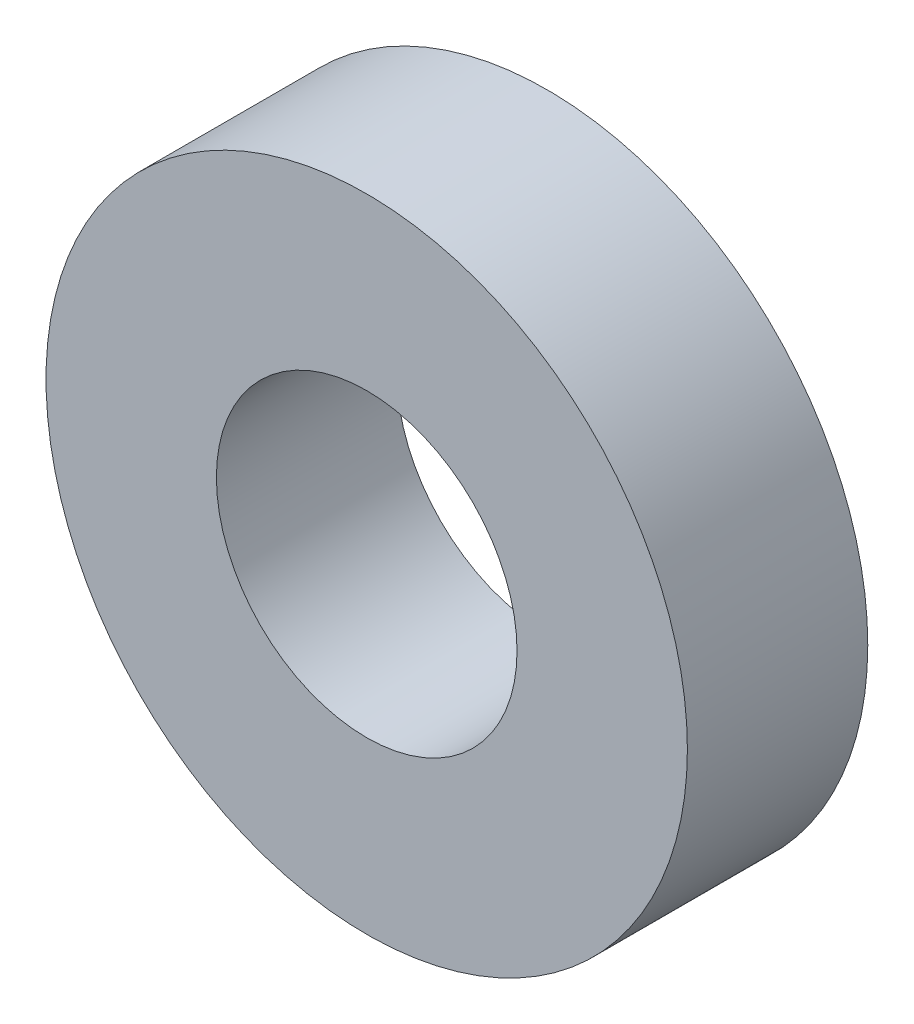
SolidWorks part; units mm, degrees
ref_plane "Front Plane" through (0, 0, 0) normal (0, 0, 1) x (1, 0, 0)
ref_plane "Top Plane" through (0, 0, 0) normal (0, 1, 0) x (1, 0, 0)
ref_plane "Right Plane" through (0, 0, 0) normal (1, 0, 0) x (0, 0, -1)
sketch "Sketch1" plane through (0, 0, 0) normal (0, 0, 1) x (1, 0, 0)
  circle A0 centre (0, 0) radius 16
  dimension "D1" = 32
extrude "Boss-Extrude1" add sketch "Sketch1" along normal blind 9
sketch "Sketch2" plane through (0, 0, 9) normal (0, 0, 1) x (1, 0, 0)
  circle A0 centre (0, 0) radius 7.5
  dimension "D1" = 15
extrude "Cut-Extrude1" cut sketch "Sketch2" against normal through all
